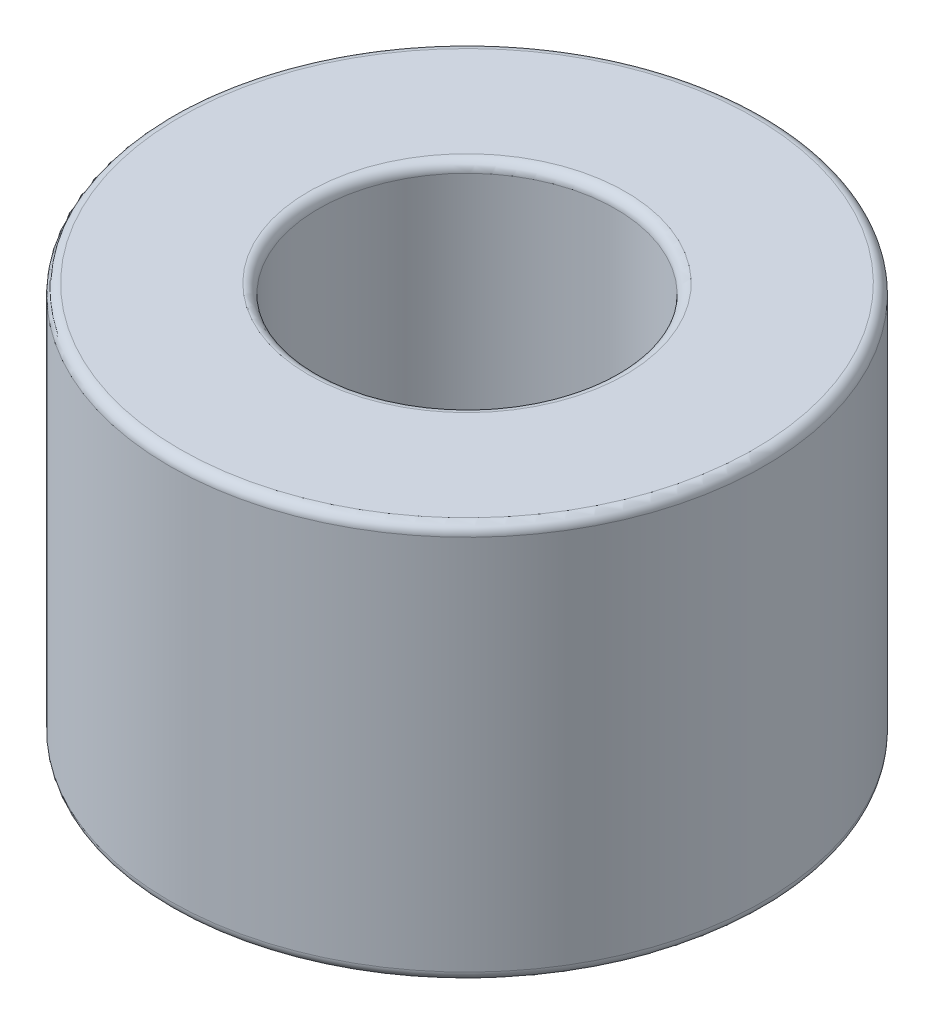
SolidWorks part; units mm, degrees
material "AISI 1020"
ref_plane "Front Plane" through (0, 0, 0) normal (0, 0, 1) x (1, 0, 0)
ref_plane "Top Plane" through (0, 0, 0) normal (0, 1, 0) x (1, 0, 0)
ref_plane "Right Plane" through (0, 0, 0) normal (1, 0, 0) x (0, 0, -1)
sketch "Sketch1" plane through (0, 0, 0) normal (0, 1, 0) x (1, 0, 0)
  circle A0 centre (0, 0) radius 3
  circle A1 centre (0, 0) radius 6
  dimension "D1" = 6
  dimension "D2" = 12
extrude "Boss-Extrude1" add sketch "Sketch1" along normal blind 8
fillet "Fillet1" radius 0.2 4 edges at (0, 8, 3) (0, 0, 3) (0, 0, 6) (0, 8, 6)
